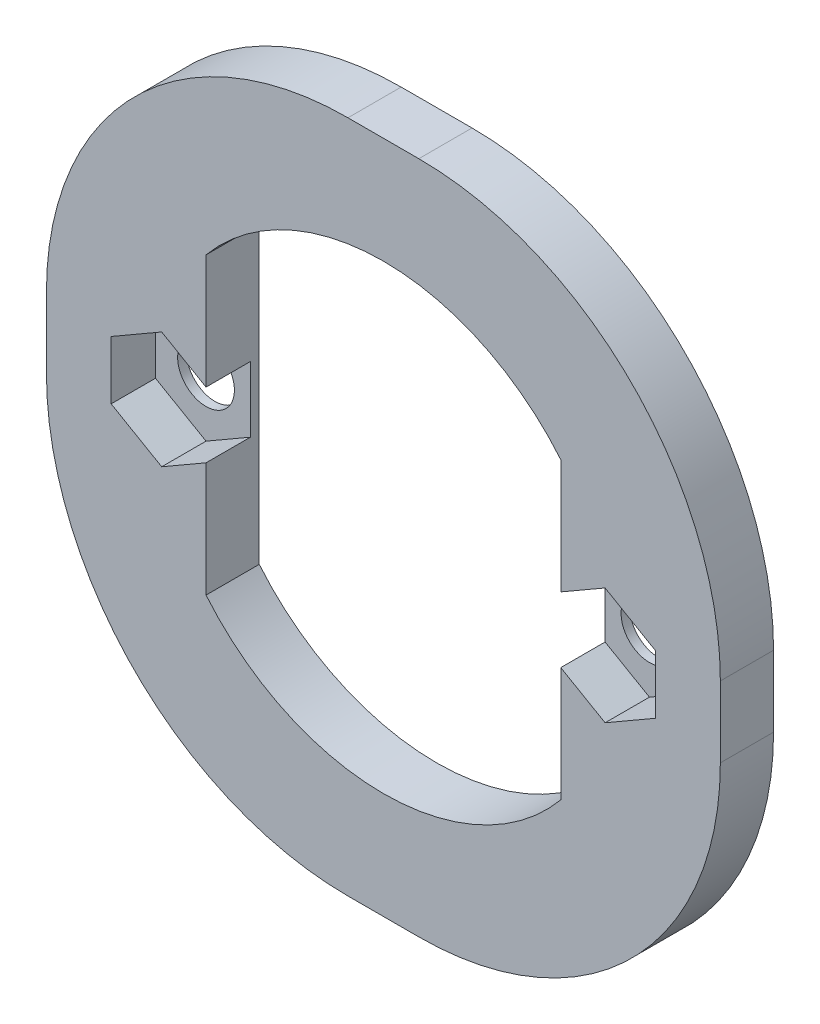
SolidWorks part; units mm, degrees
ref_plane "Płaszczyzna przednia" through (0, 0, 0) normal (0, 0, 1) x (1, 0, 0)
ref_plane "Płaszczyzna górna" through (0, 0, 0) normal (0, 1, 0) x (1, 0, 0)
ref_plane "Płaszczyzna prawa" through (0, 0, 0) normal (1, 0, 0) x (0, 0, -1)
sketch "Sketch1" plane through (0, 0, 0) normal (0, 0, 1) x (1, 0, 0)
  line L0 (0, 0) -> (11.5716, 0) construction
  line L1 (0, 0) -> (-11.5716, 0) construction
  line L2 (-9.9979, 0) -> (-8.9979, 0) construction
  line L3 (9.9979, 0) -> (8.9979, 0) construction
  line L4 (-8.9979, 0) -> (-18.9979, 0) construction
  line L5 (8.9979, 0) -> (18.9979, 0) construction
  line L6 (0, 0) -> (0, 19) construction
  line L7 (0, 0) -> (0, -19) construction
  line L8 (0, 0) -> (0, 8.0298) construction
  line L9 (-1.9979, -19) -> (1.9979, -19)
  line L10 (-18.9979, -2) -> (-18.9979, 2)
  line L11 (-1.9979, 19) -> (1.9979, 19)
  line L12 (18.9979, -2) -> (18.9979, 2)
  line L13 (-18.9979, -19) -> (18.9979, 19) construction
  line L14 (-18.9979, 19) -> (18.9979, -19) construction
  line L16 (-10, -10) -> (-9.9989, -10)
  line L17 (-10, -8.3066) -> (-10, 8.3066)
  line L18 (-10, 10) -> (-9.9989, 10)
  line L19 (10, -8.3066) -> (10, 8.3066)
  line L20 (-10, -10) -> (10, 10) construction
  line L21 (-10, 10) -> (10, -10) construction
  line L22 (9.9989, 10) -> (10, 10)
  line L23 (9.9989, -10) -> (10, -10)
  circle A0 centre (-11.5716, 0) radius 1.5737 construction
  circle A1 centre (11.5716, 0) radius 1.5737 construction
  arc A3 (-10, -8.3066) -> (10, -8.3066) centre (0, 0) ccw
  arc A4 (10, 8.3066) -> (-10, 8.3066) centre (0, 0) ccw
  arc A5 (-1.9979, -19) -> (-18.9979, -2) centre (-1.9979, -2) cw
  arc A6 (1.9979, -19) -> (18.9979, -2) centre (1.9979, -2) ccw
  arc A7 (1.9979, 19) -> (18.9979, 2) centre (1.9979, 2) cw
  arc A8 (-18.9979, 2) -> (-1.9979, 19) centre (-1.9979, 2) cw
  dimension "D1" = 1
  dimension "D5" = 17
  dimension "D2" = 1
  dimension "D3" = 20
  dimension "D4" = 20
extrude "Boss-Extrude5" add sketch "Sketch1" along normal blind 3
sketch "Sketch2" plane through (0, 0, 3) normal (0, 0, 1) x (1, 0, 0)
  line L0 (0, 0) -> (12.5, 0) construction
  line L1 (0, 0) -> (-12.5, 0) construction
  circle A2 centre (-12.5, 0) radius 1.6
  circle A3 centre (12.5, 0) radius 1.6
extrude "Cut-Extrude2" cut sketch "Sketch2" against normal through all
sketch "Sketch3" plane through (0, 0, 3) normal (0, 0, 1) x (1, 0, 0)
  line L13 (-12.5, 3.2909) -> (-15.35, 1.6454)
  line L14 (-15.35, 1.6454) -> (-15.35, -1.6454)
  line L15 (-15.35, -1.6454) -> (-12.5, -3.2909)
  line L16 (-12.5, -3.2909) -> (-9.65, -1.6454)
  line L17 (-9.65, -1.6454) -> (-9.65, 1.6454)
  line L18 (-9.65, 1.6454) -> (-12.5, 3.2909)
  line L19 (12.5, 3.2909) -> (9.65, 1.6454)
  line L20 (9.65, 1.6454) -> (9.65, -1.6454)
  line L21 (9.65, -1.6454) -> (12.5, -3.2909)
  line L22 (12.5, -3.2909) -> (15.35, -1.6454)
  line L23 (15.35, -1.6454) -> (15.35, 1.6454)
  line L24 (15.35, 1.6454) -> (12.5, 3.2909)
  circle A0 centre (-12.5, 0) radius 2.85 construction
  circle A1 centre (12.5, 0) radius 2.85 construction
extrude "Cut-Extrude3" cut sketch "Sketch3" against normal blind 2.5
sketch "Sketch4" plane through (0, 0, 0) normal (0, 0, -1) x (-1, 0, 0)
  point P0 (-12.5, 0)
  point P1 (12.5, 0)
sketch "Sketch5" plane through (0, 0, 3) normal (0, 0, 1) x (1, 0, 0)
  point P0 (-12.5, 0)
  point P1 (12.5, 0)
